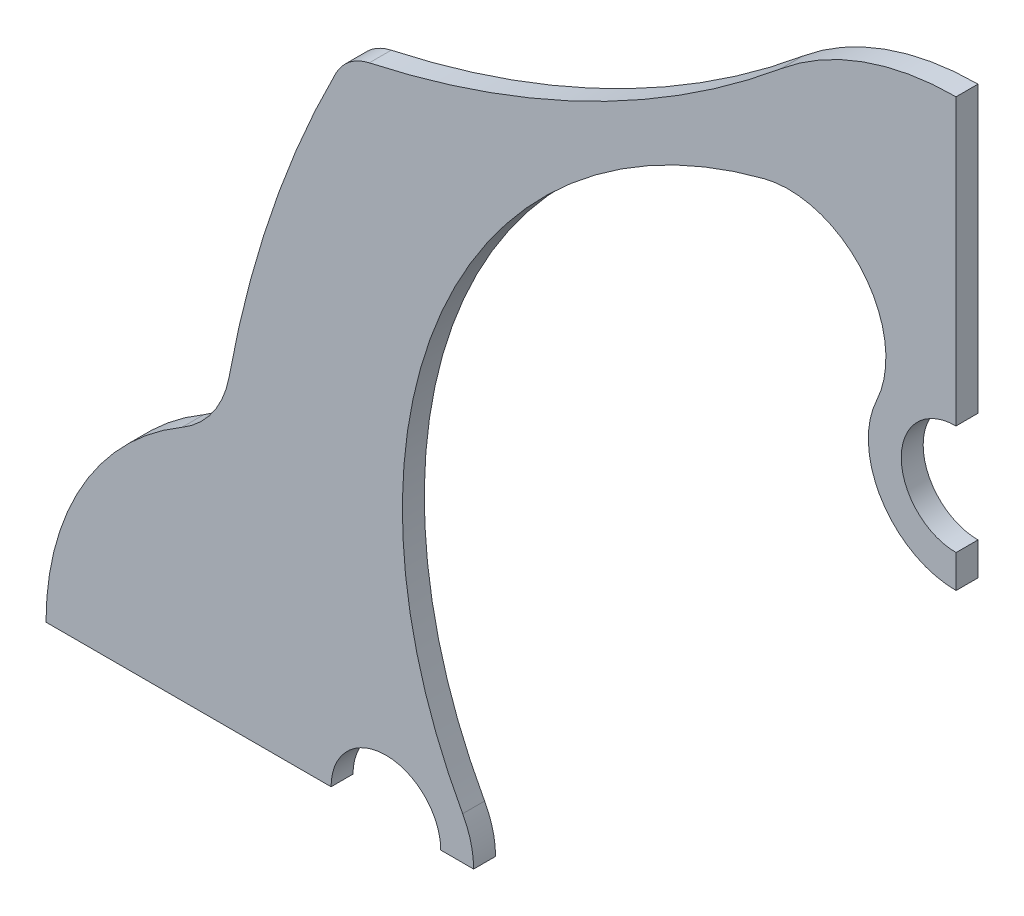
SolidWorks part; units mm, degrees
ref_plane "Ebene vorne" through (0, 0, 0) normal (0, 0, 1) x (1, 0, 0)
ref_plane "Ebene oben" through (0, 0, 0) normal (0, 1, 0) x (1, 0, 0)
ref_plane "Ebene rechts" through (0, 0, 0) normal (1, 0, 0) x (0, 0, -1)
sketch "Geometrie" plane through (0, 0, 0) normal (0, 0, 1) x (1, 0, 0)
  line L0 (-91, 0) -> (91, 0) construction
  line L1 (0, 91) -> (0, -91) construction
  circle A0 centre (0, 0) radius 91 construction
  circle A1 centre (0, 0) radius 83 construction
  circle A2 centre (0, 0) radius 52 construction
  circle A3 centre (0, 0) radius 44 construction
  circle A4 centre (0, 52) radius 5 construction
  circle A5 centre (52, 0) radius 5 construction
  circle A6 centre (0, -52) radius 5 construction
  circle A7 centre (-52, 0) radius 5 construction
  circle A8 centre (0, 0) radius 70 construction
  dimension "D1" = 182
  dimension "D4" = 166
sketch "Außenkontur" plane through (0, 0, 0) normal (0, 0, 1) x (1, 0, 0)
  line L0 (21.5873, 70.609) -> (0, 0) construction
  line L1 (0, 91) -> (0, -91) construction
  line L2 (0, 0) -> (-56.5685, 56.5685) construction
  line L3 (-91, 0) -> (91, 0) construction
  line L4 (0, 0) -> (-70.609, 21.5873) construction
  line L5 (-56.5685, 56.5685) -> (-60.7438, 48.3741) construction
  line L6 (-83, 0) -> (-57, 0)
  line L7 (-52, 0) -> (-52, 10.4246) construction
  line L9 (-47, 0) -> (-44, 0)
  line L10 (0, 83) -> (0, 57)
  line L11 (0, 44) -> (0, 47)
  circle A0 centre (0, 52) radius 8 construction
  arc A2 (-45, 3.873) -> (-17.5, 67.7772) centre (-6.5, 25.1744) cw
  circle A3 centre (0, 0) radius 70 construction
  arc A4 (-17.5, 67.7772) -> (-7.2409, 55.4014) centre (-15.2796, 59.1777) cw
  circle A5 centre (-52, 0) radius 8 construction
  circle A6 centre (0, 0) radius 44 construction
  circle A7 centre (-52, 0) radius 7 construction
  circle A8 centre (0, 52) radius 7 construction
  arc A15 (-53.5153, 58.9228) -> (-15.977, 77.2285) centre (-72.2161, 144.9128) ccw
  arc A16 (-15.977, 77.2285) -> (0, 83) centre (0, 58) cw
  arc A17 (-83, 0) -> (-70.609, 21.5873) centre (-58, 0) cw
  arc A18 (-45, 3.873) -> (-44, 0) centre (-52, 0) cw
  circle A19 centre (0, 0) radius 83 construction
  arc A22 (-53.5153, 58.9228) -> (-56.5685, 56.5685) centre (-52.559, 54.5256) ccw
  arc A23 (-7.2409, 55.4014) -> (0, 44) centre (0, 52) ccw
  arc A24 (-70.609, 21.5873) -> (-66.2931, 27.7505) centre (-75.1482, 29.3588) ccw
  arc A25 (-56.5685, 56.5685) -> (-66.2931, 27.7505) centre (36.7016, 9.045) ccw
  arc A26 (0, 57) -> (0, 47) centre (0, 52) ccw
  arc A27 (-47, 0) -> (-57, 0) centre (-52, 0) ccw
  dimension "D1" = 1
  dimension "D2" = 1
  dimension "D3" = 17
  dimension "D4" = 17
  dimension "D7" = 25
  dimension "D13" = 25
  dimension "D14" = 44
  dimension "D15" = 9
  dimension "D9" = 4.5
  dimension "D10" = 10
  dimension "D16" = 88
  dimension "D19" = 5
  dimension "D5" = 45
  dimension "D6" = 80
  dimension "D8" = 108
sketch "Innenkontur" plane through (0, 0, 0) normal (0, 0, 1) x (1, 0, 0)
  line L0 (-91, 0) -> (91, 0) construction
  arc A7 (-6.5114, 57.7634) -> (10.4363, 68.4342) centre (-8.8876, 80.3312) ccw
  arc A8 (10.4363, 68.4342) -> (5.9758, 80.2748) centre (3.6239, 72.6283) ccw
  arc A9 (5.9758, 80.2748) -> (-15.0184, 76.0748) centre (-0.6391, 58.7691) ccw
  arc A10 (-53.1965, 57.4571) -> (-15.0184, 76.0748) centre (-72.2161, 144.9128) ccw
  arc A11 (-53.1965, 57.4571) -> (-55.467, 55.263) centre (-52.559, 54.5256) ccw
  arc A12 (-55.467, 55.263) -> (-46.24, 3.9777) centre (5.6001, 39.7772) ccw
  arc A13 (-45, 0) -> (-46.24, 3.9777) centre (-52, 0) ccw
  circle A14 centre (-52, 0) radius 7 construction
  arc A15 (-7.2409, 55.4014) -> (-17.5, 67.7772) centre (-15.2796, 59.1777) ccw construction
  circle A16 centre (0, 52) radius 7 construction
  arc A17 (-53.5153, 58.9228) -> (-15.977, 77.2285) centre (-72.2161, 144.9128) ccw construction
  arc A18 (-53.5153, 58.9228) -> (-56.5685, 56.5685) centre (-52.559, 54.5256) ccw construction
  dimension "D1" = 63
  dimension "D2" = 3
  dimension "D4" = 22.5
  dimension "D5" = 8
  dimension "D6" = 22.6925
extrude "Linear austragen1" add sketch "Außenkontur" along normal mid plane 2
sketch "Skizze1" plane through (0, 0, 0) normal (0, 1, 0) x (1, 0, 0)
  line L0 (0, -9.3188) -> (0, 15.5291) construction
